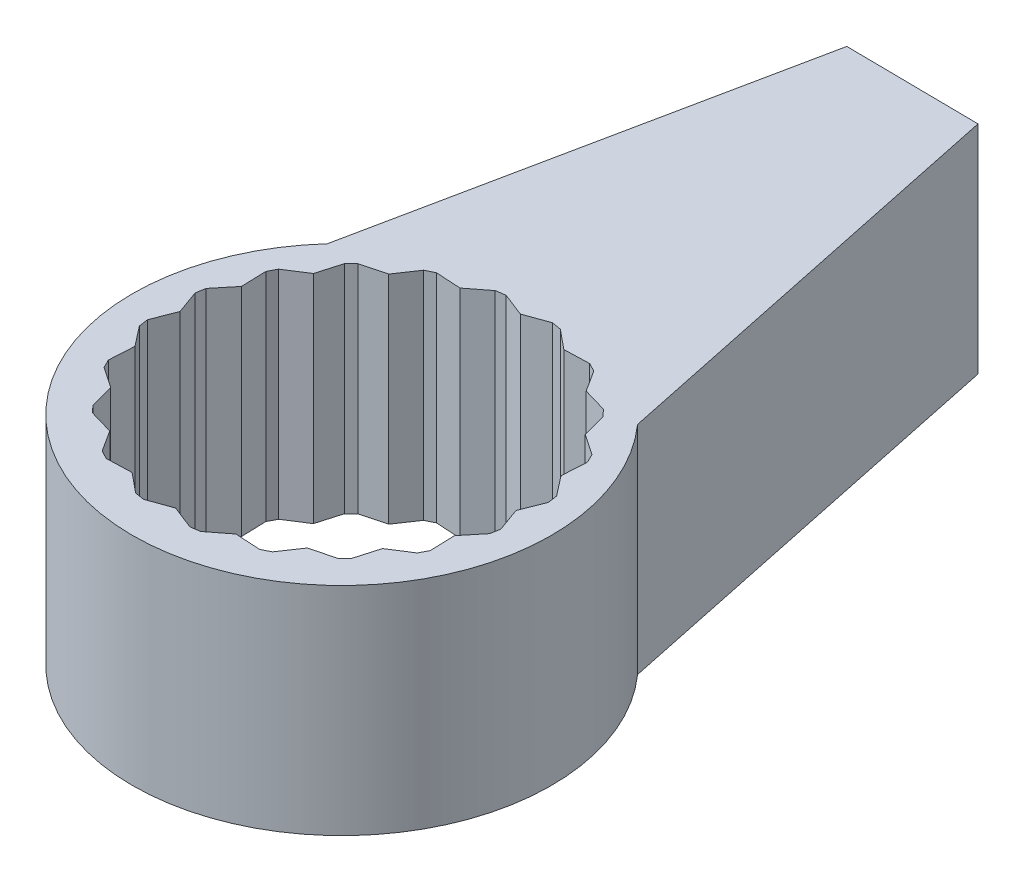
SolidWorks part; units mm, degrees
ref_plane "Ön Düzlem" through (0, 0, 0) normal (0, 0, 1) x (1, 0, 0)
ref_plane "Üst Düzlem" through (0, 0, 0) normal (0, 1, 0) x (1, 0, 0)
ref_plane "Sağ Düzlem" through (0, 0, 0) normal (1, 0, 0) x (0, 0, -1)
sketch "Çizim2" plane through (0, 0, 0) normal (0, 1, 0) x (1, 0, 0)
  line L0 (-2.2416, 1.9938) -> (-0.9999, 8.0117)
  line L1 (2.2584, 1.9748) -> (0.9999, 7.9893)
  line L2 (-0.9999, 8.0117) -> (0.9999, 7.9893)
  line L3 (-2.1492, 1.9471) -> (-0.9187, 7.9108)
  line L4 (-0.9187, 7.9108) -> (0.9185, 7.8902)
  line L5 (2.1659, 1.9284) -> (0.9185, 7.8902)
  arc A0 (-2.2416, 1.9938) -> (2.2584, 1.9748) centre (0, 0) ccw
  arc A1 (-2.1492, 1.9471) -> (2.1659, 1.9284) centre (0, 0) ccw
  point P4 (0, 8.0005)
  dimension "D2" = 3
  dimension "D1" = 1.9999
  dimension "D3" = 4.5
  dimension "D4" = 6.0145
  dimension "D5" = 8
  dimension "D6" = 0.1
extrude "Yükseklik-Ekstrüzyon1" add sketch "Çizim2" along normal blind 3 contours L3 A1 L5 L4
sketch "Çizim3" plane through (0, 3, -0.0832) normal (0, 1, 0) x (1, 0, 0)
  line L60 (-1.6969, 1.8374) -> (-1.7921, 1.7446)
  line L61 (-1.7921, 1.7446) -> (-1.8888, 1.4107)
  line L62 (-1.8888, 1.4107) -> (-2.1814, 1.2231)
  line L63 (-2.1814, 1.2231) -> (-2.2433, 1.1054)
  line L64 (-2.2433, 1.1054) -> (-2.2321, 0.758)
  line L65 (-2.2321, 0.758) -> (-2.4524, 0.4892)
  line L66 (-2.4524, 0.4892) -> (-2.4749, 0.3582)
  line L67 (-2.4749, 0.3582) -> (-2.3568, 0.0312)
  line L68 (-2.3568, 0.0312) -> (-2.4833, -0.2925)
  line L69 (-2.4833, -0.2925) -> (-2.4642, -0.4241)
  line L70 (-2.4642, -0.4241) -> (-2.2509, -0.6986)
  line L71 (-2.2509, -0.6986) -> (-2.2711, -1.0456)
  line L72 (-2.2711, -1.0456) -> (-2.2123, -1.1648)
  line L73 (-2.2123, -1.1648) -> (-1.9246, -1.3599)
  line L74 (-1.9246, -1.3599) -> (-1.8366, -1.6962)
  line L75 (-1.8366, -1.6962) -> (-1.7438, -1.7914)
  line L76 (-1.7438, -1.7914) -> (-1.41, -1.888)
  line L77 (-1.41, -1.888) -> (-1.2224, -2.1807)
  line L78 (-1.2224, -2.1807) -> (-1.1047, -2.2425)
  line L79 (-1.1047, -2.2425) -> (-0.7573, -2.2313)
  line L80 (-0.7573, -2.2313) -> (-0.4884, -2.4516)
  line L81 (-0.4884, -2.4516) -> (-0.3574, -2.4741)
  line L82 (-0.3574, -2.4741) -> (-0.0305, -2.3561)
  line L83 (-0.0305, -2.3561) -> (0.2933, -2.4825)
  line L84 (0.2933, -2.4825) -> (0.4249, -2.4634)
  line L85 (0.4249, -2.4634) -> (0.6993, -2.2501)
  line L86 (0.6993, -2.2501) -> (1.0463, -2.2704)
  line L87 (1.0463, -2.2704) -> (1.1655, -2.2115)
  line L88 (1.1655, -2.2115) -> (1.3606, -1.9239)
  line L89 (1.3606, -1.9239) -> (1.6969, -1.8359)
  line L90 (1.6969, -1.8359) -> (1.7921, -1.7431)
  line L91 (1.7921, -1.7431) -> (1.8888, -1.4092)
  line L92 (1.8888, -1.4092) -> (2.1814, -1.2216)
  line L93 (2.1814, -1.2216) -> (2.2433, -1.1039)
  line L94 (2.2433, -1.1039) -> (2.2321, -0.7565)
  line L95 (2.2321, -0.7565) -> (2.4524, -0.4877)
  line L96 (2.4524, -0.4877) -> (2.4749, -0.3567)
  line L97 (2.4749, -0.3567) -> (2.3568, -0.0297)
  line L98 (2.3568, -0.0297) -> (2.4833, 0.294)
  line L99 (2.4833, 0.294) -> (2.4642, 0.4256)
  line L100 (2.4642, 0.4256) -> (2.2509, 0.7001)
  line L101 (2.2509, 0.7001) -> (2.2711, 1.0471)
  line L102 (2.2711, 1.0471) -> (2.2123, 1.1663)
  line L103 (2.2123, 1.1663) -> (1.9246, 1.3614)
  line L104 (1.9246, 1.3614) -> (1.8366, 1.6977)
  line L105 (1.8366, 1.6977) -> (1.7438, 1.7929)
  line L106 (1.7438, 1.7929) -> (1.41, 1.8895)
  line L107 (1.41, 1.8895) -> (1.2224, 2.1822)
  line L108 (1.2224, 2.1822) -> (1.1047, 2.2441)
  line L109 (1.1047, 2.2441) -> (0.7573, 2.2328)
  line L110 (0.7573, 2.2328) -> (0.4884, 2.4531)
  line L111 (0.4884, 2.4531) -> (0.3574, 2.4756)
  line L112 (0.3574, 2.4756) -> (0.0305, 2.3576)
  line L113 (0.0305, 2.3576) -> (-0.2933, 2.484)
  line L114 (-0.2933, 2.484) -> (-0.4249, 2.4649)
  line L115 (-0.4249, 2.4649) -> (-0.6993, 2.2516)
  line L116 (-0.6993, 2.2516) -> (-1.0463, 2.2719)
  line L117 (-1.0463, 2.2719) -> (-1.1655, 2.2131)
  line L118 (-1.1655, 2.2131) -> (-1.3606, 1.9254)
  line L119 (-1.3606, 1.9254) -> (-1.6969, 1.8374)
  circle A1 centre (0, 0.0008) radius 2.5005
extrude "Kes-Ekstrüzyon1" cut sketch "Çizim3" against normal blind 3 contours L118 L119 L60 L61 L62 L63 L64 L65 L66 L67 L68 L69 L70 L71 L72 L73 L74 L75 L76 L77 L78 L79 L80 L81 L82 L83 L84 L85 L86 L87 L88 L89 L90 L91 L92 L93 L94 L95 L96 L97 L98 L99 L100 L101 L102 L103 L104 L105 L106 L107 L108
